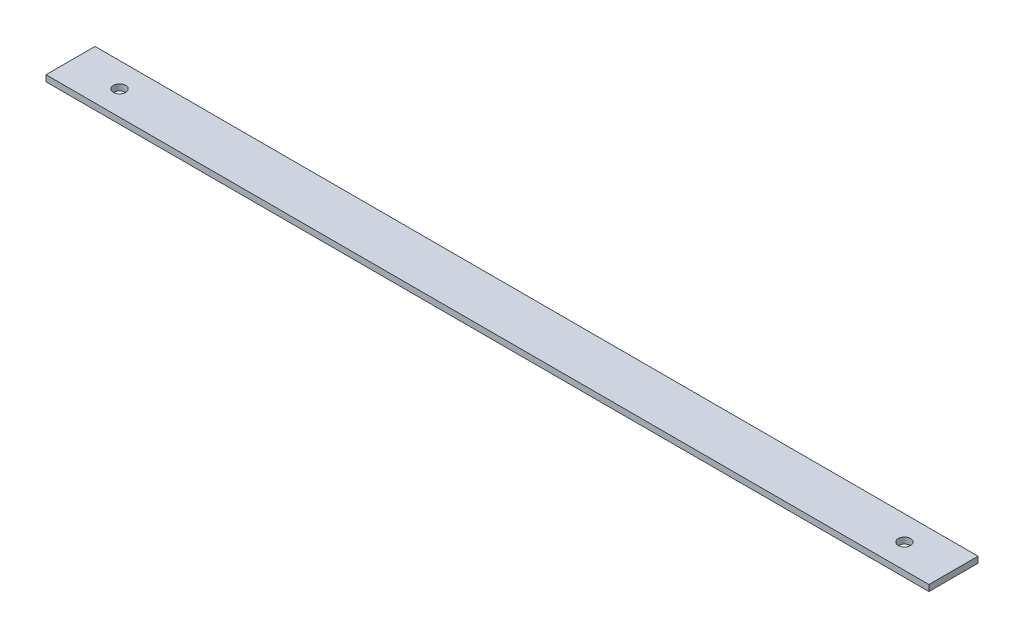
SolidWorks part; units mm, degrees
ref_plane "Front" through (0, 0, 0) normal (0, 0, 1) x (1, 0, 0)
ref_plane "Top" through (0, 0, 0) normal (0, 1, 0) x (1, 0, 0)
ref_plane "Right" through (0, 0, 0) normal (1, 0, 0) x (0, 0, -1)
sketch "Sketch1" plane through (0, 0, 0) normal (0, 1, 0) x (1, 0, 0)
  line L1 (0, 0) -> (457.2, 0)
  line L2 (0, 0) -> (0, 25.4)
  line L3 (0, 25.4) -> (457.2, 25.4)
  line L4 (457.2, 0) -> (457.2, 25.4)
  line L5 (0, 0) -> (457.2, 25.4) construction
  line L6 (0, 25.4) -> (457.2, 0) construction
  point P4 (228.6, 12.7)
  dimension "D1" = 25.4
  dimension "D2" = 457.2
extrude "Boss-Extrude1" add sketch "Sketch1" along normal blind 3.175
sketch "Sketch2" plane through (0, 3.175, 0) normal (0, 1, 0) x (1, 0, 0)
  line L0 (457.2, 0) -> (457.2, 25.4) construction
  line L1 (0, 25.4) -> (0, 0) construction
  line L3 (0, 12.7) -> (25.4, 12.7) construction
  line L4 (457.2, 12.7) -> (431.8, 12.7) construction
  circle A0 centre (431.8, 12.7) radius 3.175
  circle A2 centre (25.4, 12.7) radius 3.175
  dimension "D1" = 6.35
  dimension "D5" = 6.35
  dimension "D2" = 406.4
extrude "Cut-Extrude1" cut sketch "Sketch2" against normal through all
